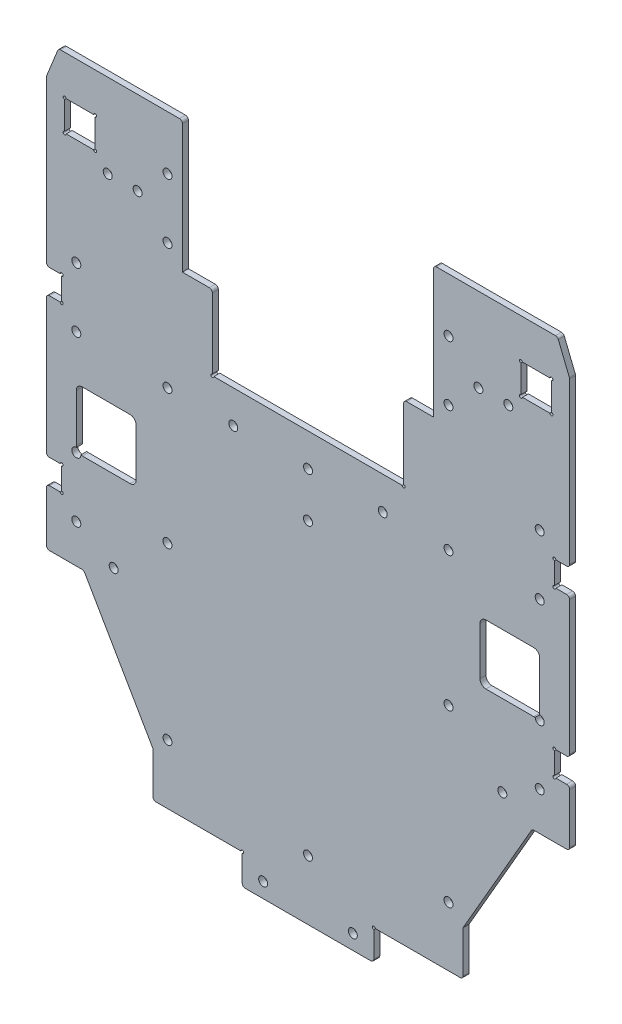
SolidWorks part; units mm, degrees
material "环氧板3240"
ref_plane "前视基准面" through (0, 0, 0) normal (0, 0, 1) x (1, 0, 0)
ref_plane "上视基准面" through (0, 0, 0) normal (0, 1, 0) x (1, 0, 0)
ref_plane "右视基准面" through (0, 0, 0) normal (1, 0, 0) x (0, 0, -1)
other "Configuration Table"
sketch "草图1" plane through (0, 0, 0) normal (0, 0, 1) x (1, 0, 0)
  line L5 (-87.5, 69) -> (-87.5, -77.9)
  line L7 (-51.9, -132.9) -> (51.9, -132.9) construction
  line L10 (0, 0) -> (0, -132.9) construction
  line L12 (87.5, 69) -> (87.5, -77.9)
  line L15 (87.5, 69) -> (42, 69)
  line L16 (42, 69) -> (42, 0)
  line L18 (-42, 0) -> (-42, 69)
  line L19 (-42, 69) -> (-87.5, 69)
  line L20 (87.5, -11) -> (-87.5, -11) construction
  line L21 (-47, 69) -> (-47, -132.9) construction
  line L22 (47, 69) -> (47, -132.9) construction
  line L23 (22, -138) -> (-22, -138) construction
  line L24 (-22, -132.9) -> (-22, -143)
  line L25 (-22, -143) -> (22, -143)
  line L26 (22, -143) -> (22, -132.9)
  line L27 (81.4, 45.6) -> (71.2, 45.6)
  line L28 (0, -132.9) -> (0, -143) construction
  line L29 (51.9, -132.9) -> (22, -132.9)
  line L30 (-22, -132.9) -> (-51.9, -132.9)
  line L31 (-81.4, 55.8) -> (-71.2, 55.8)
  line L32 (-81.4, 55.8) -> (-81.4, 45.6)
  line L33 (-81.4, 45.6) -> (-71.2, 45.6)
  line L34 (-71.2, 55.8) -> (-71.2, 45.6)
  line L35 (-81.4, 55.8) -> (-71.2, 45.6) construction
  line L36 (-81.4, 45.6) -> (-71.2, 55.8) construction
  line L37 (71.2, 55.8) -> (71.2, 45.6)
  line L38 (81.4, 55.8) -> (71.2, 55.8)
  line L39 (81.4, 55.8) -> (81.4, 45.6)
  line L41 (-42, 0) -> (42, 0)
  line L44 (-47, -56) -> (47, -56) construction
  line L48 (-51.9, -117.9) -> (-51.9, -132.9)
  line L51 (51.9, -117.9) -> (51.9, -132.9)
  line L52 (-47, 41) -> (-67, 41) construction
  line L53 (87.5, -77.9) -> (74.994, -77.9)
  line L54 (74.994, -77.9) -> (51.9, -117.9)
  line L55 (-87.5, -77.9) -> (-74.994, -77.9)
  line L56 (-74.994, -77.9) -> (-51.9, -117.9)
  circle A1 centre (-25, -11) radius 1.5
  circle A2 centre (0, -26) radius 1.5
  circle A3 centre (0, -41) radius 1.5 construction
  circle A4 centre (-47, -11) radius 1.5
  circle A9 centre (-15, -138) radius 1.5
  circle A10 centre (0, -108) radius 1.5 construction
  circle A12 centre (0, -123) radius 1.5
  circle A13 centre (-47, -11) radius 2.5 construction
  circle A14 centre (47, -11) radius 1.5
  circle A16 centre (25, -11) radius 1.5
  circle A18 centre (15, -138) radius 1.5
  circle A20 centre (0, -138) radius 1.5 construction
  circle A21 centre (0, -11) radius 1.5
  circle A22 centre (-47, 51) radius 1.5
  circle A23 centre (-47, 41) radius 1.5 construction
  circle A24 centre (47, 41) radius 1.5 construction
  circle A25 centre (47, 51) radius 1.5
  circle A26 centre (-47, -113) radius 1.5
  circle A27 centre (-47, -98) radius 1.5 construction
  circle A28 centre (-47, -56) radius 1.5
  circle A29 centre (47, -56) radius 1.5
  circle A30 centre (47, -113) radius 1.5
  circle A31 centre (47, -98) radius 1.5 construction
  circle A32 centre (0, -56) radius 1.5 construction
  circle A33 centre (-47, 31) radius 1.5
  circle A34 centre (-67, 41) radius 1.5
  circle A35 centre (-57, 41) radius 1.5
  circle A36 centre (57, 41) radius 1.5
  circle A37 centre (67, 41) radius 1.5
  circle A38 centre (-47, -11) radius 1.5 construction
  circle A39 centre (47, -11) radius 1.5 construction
  circle A40 centre (47, 31) radius 1.5
  point P61 (-76.3, 50.7)
  dimension "D11" = 3
  dimension "D13" = 55
  dimension "D14" = 5
  dimension "D15" = 15
  dimension "D16" = 25
  dimension "D18" = 15
  dimension "D19" = 15
  dimension "D21" = 15
  dimension "D22" = 3
  dimension "D23" = 30
  dimension "D29" = 10
  dimension "D30" = 179
  dimension "D31" = 15
  dimension "D32" = 25
  dimension "D33" = 42
  dimension "D34" = 3
  dimension "D38" = 10
  dimension "D39" = 127
  dimension "D40" = 10
  dimension "D41" = 10
  dimension "D1" = 175
  dimension "D5" = 10.1
  dimension "D6" = 212
  dimension "D7" = 120
  dimension "D8" = 44
  dimension "D9" = 5
  dimension "D10" = 94
  dimension "D12" = 0
  dimension "D17" = 132
  dimension "D20" = 15
  dimension "D24" = 188.6
  dimension "D25" = 24.2
  dimension "D26" = 10.2
  dimension "D27" = 10.2
  dimension "D28" = 11
  dimension "D35" = 4.9
  dimension "D36" = 84
extrude "凸台-拉伸3" add sketch "草图1" along normal blind 2
sketch "草图3" plane through (0, 0, 2) normal (0, 0, 1) x (1, 0, 0)
  line L0 (87.5, 69) -> (87.5, -77.9) construction
  line L1 (87.5, 4.1) -> (82.4, 4.1)
  line L2 (87.5, 4.1) -> (87.5, -4.1)
  line L3 (87.5, -4.1) -> (82.4, -4.1)
  line L4 (82.4, 4.1) -> (82.4, -4.1)
  line L5 (87.5, 4.1) -> (82.4, -4.1) construction
  line L6 (87.5, -4.1) -> (82.4, 4.1) construction
  line L7 (77.5, -45) -> (77.5, -65) construction
  line L8 (0, 0) -> (0, -143) construction
  line L9 (-87.5, -4.1) -> (-82.4, -4.1)
  line L10 (-82.4, 4.1) -> (-82.4, -4.1)
  line L11 (-87.5, 4.1) -> (-82.4, 4.1)
  line L12 (-87.5, 4.1) -> (-87.5, -4.1)
  line L13 (-87.5, -59.1) -> (-82.4, -59.1)
  line L14 (87.5, -59.1) -> (82.4, -59.1)
  line L15 (87.5, -59.1) -> (87.5, -50.9)
  line L16 (87.5, -50.9) -> (82.4, -50.9)
  line L17 (82.4, -59.1) -> (82.4, -50.9)
  line L18 (87.5, -59.1) -> (82.4, -50.9) construction
  line L19 (87.5, -50.9) -> (82.4, -59.1) construction
  line L20 (-87.5, -59.1) -> (-87.5, -50.9)
  line L21 (-82.4, -59.1) -> (-82.4, -50.9)
  line L22 (-87.5, -50.9) -> (-82.4, -50.9)
  line L23 (82.4, 0) -> (77.5, 0) construction
  line L24 (82.4, -55) -> (77.5, -55) construction
  line L25 (77.5, -10) -> (77.5, -45) construction
  line L26 (77.5, 10) -> (77.5, -10) construction
  line L27 (83.4597, 69) -> (87.5, 59)
  line L28 (87.5, 69) -> (42, 69) construction
  line L29 (87.5, 59) -> (87.5, 69)
  line L30 (87.5, 69) -> (83.4597, 69)
  line L31 (-87.5, 59) -> (-87.5, 69)
  line L32 (-83.4597, 69) -> (-87.5, 59)
  line L33 (-87.5, 69) -> (-83.4597, 69)
  line L34 (-22, -143) -> (22, -143) construction
  circle A0 centre (77.5, 10) radius 1.5
  circle A1 centre (77.5, -10) radius 1.5
  circle A2 centre (77.5, -45) radius 1.5
  circle A3 centre (77.5, -65) radius 1.5
  circle A4 centre (-77.5, -45) radius 1.5
  circle A5 centre (-77.5, -65) radius 1.5
  circle A6 centre (-77.5, -10) radius 1.5
  circle A7 centre (-77.5, 10) radius 1.5
  point P4 (84.95, 0)
  point P15 (84.95, -4.1)
  point P22 (84.95, -55)
  dimension "D5" = 3
  dimension "D6" = 20
  dimension "D7" = 20
  dimension "D1" = 8.2
  dimension "D2" = 5.1
  dimension "D3" = 88
  dimension "D4" = 46.8
  dimension "D8" = 10
  dimension "D10" = 22
  dimension "D11" = 10
extrude "切除-拉伸2" cut sketch "草图3" against normal through all
sketch "草图4" plane through (0, 0, 0) normal (0, 0, -1) x (-1, 0, 0)
  line L0 (0, 0) -> (0, 26.8526) construction
  line L1 (-42, 0) -> (-32, 0)
  line L2 (-42, 0) -> (-42, 25)
  line L3 (-42, 25) -> (-32, 25)
  line L4 (-32, 0) -> (-32, 25)
  line L5 (-42, 0) -> (-32, 25) construction
  line L6 (-42, 25) -> (-32, 0) construction
  line L7 (42, 25) -> (32, 25)
  line L8 (32, 0) -> (32, 25)
  line L9 (42, 0) -> (32, 0)
  line L10 (42, 0) -> (42, 25)
  line L11 (42, 0) -> (-42, 0) construction
  point P4 (-37, 12.5)
  dimension "D1" = 10
  dimension "D2" = 25
  dimension "D3" = 10
extrude "凸台-拉伸4" add sketch "草图4" against normal blind 2
sketch "草图2" plane through (0, 0, 2) normal (0, 0, 1) x (1, 0, 0)
  line L0 (0, 0) -> (0, -11) construction
  line L1 (82.4, 4.1) -> (82.4, -4.1) construction
  circle A0 centre (-81.4, 45.6) radius 0.5
  circle A1 centre (-81.4, 55.8) radius 0.5
  circle A2 centre (-71.2, 45.6) radius 0.5
  circle A3 centre (-71.2, 55.8) radius 0.5
  circle A4 centre (71.2, 55.8) radius 0.5
  circle A5 centre (71.2, 45.6) radius 0.5
  circle A6 centre (81.4, 55.8) radius 0.5
  circle A7 centre (81.4, 45.6) radius 0.5
  circle A8 centre (82.4, 4.1) radius 0.5
  circle A9 centre (82.4, -4.1) radius 0.5
  circle A10 centre (82.4, -50.9) radius 0.5
  circle A11 centre (82.4, -59.1) radius 0.5
  circle A12 centre (22, -132.9) radius 0.5
  circle A13 centre (-82.4, -59.1) radius 0.5
  circle A14 centre (-82.4, -50.9) radius 0.5
  circle A15 centre (-82.4, -4.1) radius 0.5
  circle A16 centre (-82.4, 4.1) radius 0.5
  circle A17 centre (-22, -132.9) radius 0.5
  circle A18 centre (32, 0) radius 0.5
  circle A19 centre (-32, 0) radius 0.5
  dimension "D1" = 1
extrude "切除-拉伸1" cut sketch "草图2" against normal through all
fillet "圆角1" radius 1 24 edges at (-74.994, -77.9, 1) (-87.5, -77.9, 1) (74.994, -77.9, 1) (87.5, -77.9, 1) (-87.5, 4.1, 1) (-87.5, -4.1, 1) (-87.5, -50.9, 1) (-87.5, -59.1, 1) (-51.9, -132.9, 1) (-22, -143, 1) (22, -143, 1) (51.9, -132.9, 1) (87.5, -50.9, 1) (87.5, -59.1, 1) (87.5, -4.1, 1) (87.5, 4.1, 1) (87.5, 59, 1) (83.4597, 69, 1) (42, 69, 1) (32, 25, 1) (-32, 25, 1) (-42, 69, 1) (-87.5, 59, 1) (-83.4597, 69, 1)
sketch "草图5" plane through (0, 0, 2) normal (0, 0, 1) x (1, 0, 0)
  line L0 (-87.5, -5.1) -> (-87.5, -49.9) construction
  line L1 (-75.5, -25) -> (-59.5, -25)
  line L2 (-77.5, -27) -> (-77.5, -43)
  line L3 (-75.5, -45) -> (-59.5, -45)
  line L4 (-57.5, -27) -> (-57.5, -43)
  line L5 (-21, -143) -> (21, -143) construction
  line L6 (0, 0) -> (0, -143) construction
  line L8 (75.5, -45) -> (59.5, -45)
  line L9 (57.5, -27) -> (57.5, -43)
  line L10 (75.5, -25) -> (59.5, -25)
  line L11 (77.5, -27) -> (77.5, -43)
  arc A0 (-77.5, -27) -> (-75.5, -25) centre (-75.5, -27) cw
  arc A1 (-59.5, -45) -> (-57.5, -43) centre (-59.5, -43) ccw
  arc A2 (-57.5, -27) -> (-59.5, -25) centre (-59.5, -27) ccw
  arc A3 (-75.5, -45) -> (-77.5, -43) centre (-75.5, -43) cw
  arc A4 (59.5, -45) -> (57.5, -43) centre (59.5, -43) cw
  arc A5 (57.5, -27) -> (59.5, -25) centre (59.5, -27) cw
  arc A6 (77.5, -27) -> (75.5, -25) centre (75.5, -27) ccw
  arc A7 (75.5, -45) -> (77.5, -43) centre (75.5, -43) ccw
  point P11 (-77.5, -25)
  point P16 (-57.5, -25)
  point P19 (-77.5, -45)
  dimension "D5" = 2
  dimension "D1" = 20
  dimension "D2" = 20
  dimension "D3" = 30
  dimension "D4" = 118
extrude "切除-拉伸3" cut sketch "草图5" against normal blind 10
sketch "草图6" plane through (0, 0, 2) normal (0, 0, 1) x (1, 0, 0)
  line L0 (0, 0) -> (0, -123) construction
  line L1 (-31.5, 0) -> (31.5, 0) construction
  circle A0 centre (-65, -72.2) radius 1.5
  circle A1 centre (-77.5, -65) radius 1.5 construction
  circle A2 centre (65, -72.2) radius 1.5
  dimension "D1" = 3
  dimension "D2" = 7.2
  dimension "D3" = 130
extrude "切除-拉伸4" cut sketch "草图6" against normal blind 10
